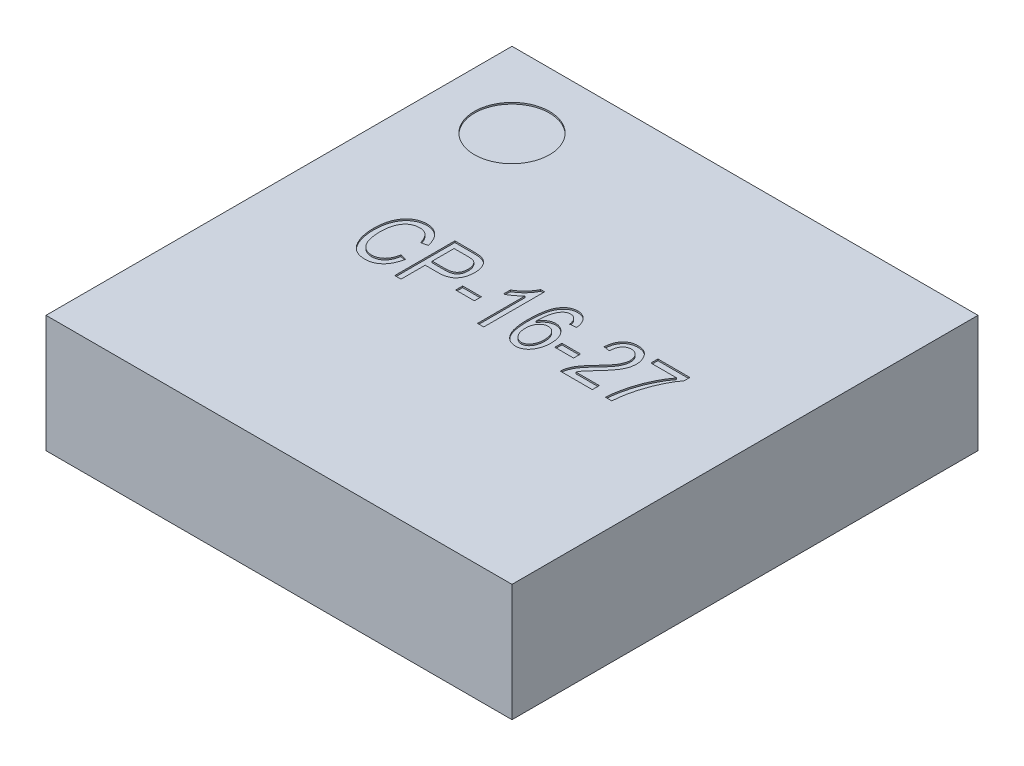
SolidWorks part; units mm, degrees
ref_plane "Front Plane" through (0, 0, 0) normal (0, 0, 1) x (1, 0, 0)
ref_plane "Top Plane" through (0, 0, 0) normal (0, 1, 0) x (1, 0, 0)
ref_plane "Right Plane" through (0, 0, 0) normal (1, 0, 0) x (0, 0, -1)
sketch "Sketch1" plane through (0, 0, 0) normal (0, 1, 0) x (1, 0, 0)
  line L1 (-1.55, -1.55) -> (1.55, -1.55)
  line L2 (-1.55, -1.55) -> (-1.55, 1.55)
  line L3 (-1.55, 1.55) -> (1.55, 1.55)
  line L4 (1.55, -1.55) -> (1.55, 1.55)
  line L5 (-1.55, -1.55) -> (1.55, 1.55) construction
  line L6 (-1.55, 1.55) -> (1.55, -1.55) construction
  point P0 (0, 0)
  dimension "D1" = 3.1
extrude "Boss-Extrude1" add sketch "Sketch1" along normal blind 0.78
sketch "Sketch2" plane through (0, 0.78, 0) normal (0, 1, 0) x (1, 0, 0)
  line L0 (-1.55, 1.55) -> (-1.55, -1.55) construction
  line L1 (1.55, 1.55) -> (-1.55, 1.55) construction
  circle A0 centre (-1.05, 1.05) radius 0.25
  dimension "D3" = 0.5
  dimension "D1" = 0.5
  dimension "D2" = 0.5
extrude "Cut-Extrude1" cut sketch "Sketch2" against normal blind 0.01
sketch "Sketch3" plane through (0, 0.78, 0) normal (0, 1, 0) x (1, 0, 0)
  line L0 (-0.9878, -0.161) -> (1.3, -0.161) construction
  text T0 "CP-16-27\r\n" font "Arial Narrow" height 0.4
  point P3 (-0.9006, -0.1544)
  point P4 (-0.9878, -0.1564)
  point P5 (1.3, -0.161)
extrude "Cut-Extrude2" cut sketch "Sketch3" against normal blind 0.01
